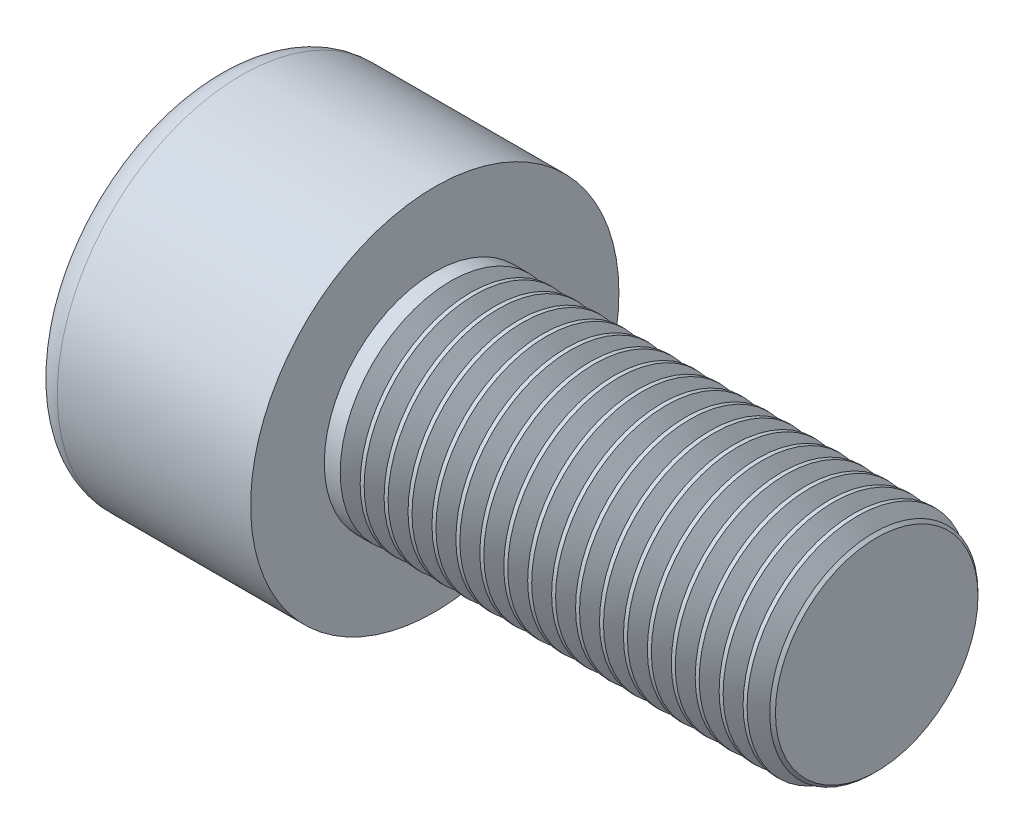
SolidWorks part; units mm, degrees
ref_plane "Front" through (0, 0, 0) normal (0, 0, 1) x (1, 0, 0)
ref_plane "Top" through (0, 0, 0) normal (0, 1, 0) x (1, 0, 0)
ref_plane "Right" through (0, 0, 0) normal (1, 0, 0) x (0, 0, -1)
sketch "Sketch1" plane through (0, 0, 0) normal (1, 0, 0) x (0, 0, -1)
  circle A0 centre (0, 0) radius 5
  dimension "dk" = 10
extrude "BaseHead" add sketch "Sketch1" along normal blind 6
sketch "Sketch2" plane through (6, 0, 0) normal (1, 0, 0) x (0, 0, -1)
  circle A0 centre (0, 0) radius 3
  dimension "d" = 6
extrude "BaseBody" add sketch "Sketch2" along normal blind 12
cosmetic thread "ThreadCosmetic1" [suppressed] parameters "b"=12, "D2"=4.917
sketch "Sketch3" plane through (0, 0, 0) normal (1, 0, 0) x (0, 0, -1)
  line L1 (2.8868, 0) -> (1.4434, 2.5)
  line L2 (1.4434, 2.5) -> (-1.4434, 2.5)
  line L3 (-1.4434, 2.5) -> (-2.8868, 0)
  line L4 (-2.8868, 0) -> (-1.4434, -2.5)
  line L5 (-1.4434, -2.5) -> (1.4434, -2.5)
  line L6 (1.4434, -2.5) -> (2.8868, 0)
  circle A0 centre (0, 0) radius 2.5 construction
  dimension "s" = 5
  dimension "e" = 5.7735
extrude "HexagonSocket" cut sketch "Sketch3" along normal blind 3
sketch "Sketch4" plane through (-4.1961, 0.75, 0) normal (0, 0, 1) x (-1, 0, 0)
  line L0 (-7.1961, 3.25) -> (-8.6395, 0.75)
  line L2 (-8.6395, 0.75) -> (-7.1961, 0.75)
  line L3 (-7.1961, 0.75) -> (-7.1961, 3.25)
  line L4 (-5.0351, 0.75) -> (0.839, 0.75) construction
  line L5 (-22.1961, 0.75) -> (-10.1961, 0.75) construction
  line L6 (-10.1961, 0.75) -> (-4.1961, 0.75) construction
  dimension "m" = 60
revolve "Cut-Revolve1" cut sketch "Sketch4" angle 360 about L4
fillet "HeadFillet" [suppressed] radius 0.25
fillet "TopFillet" radius 0.75 1 edges at (0, 0, -5)
chamfer "Chamfer1" distance 0.25 angle 45 1 edges at (18, 0, -3)
sketch "Sketch5" plane through (0, 0, 0) normal (0, 0, 1) x (1, 0, 0)
  line L0 (17.75, 2.531) -> (18.0208, 3)
  line L1 (18.0208, 3) -> (18.0208, 3.5415)
  line L2 (18.0208, 3.5415) -> (17.4793, 3.5415)
  line L3 (17.4793, 3.5415) -> (17.4793, 3)
  line L4 (17.4793, 3) -> (17.75, 2.531)
  line L5 (0, 0) -> (7.8886, 0) construction
  line L6 (17.75, -3) -> (17.75, 3) construction
  dimension "D1" = 6
  dimension "D2" = 0.5415
revolve "Cut-Revolve10" cut sketch "Sketch5" angle 360 about L5
pattern_linear "LPattern10" count 18 spacing 0.6498 along (-1, 0, 0) of "Cut-Revolve10"
equation "\"r1@TopFillet\" = \"d@Sketch2\" / 8"
equation "\"D1@Chamfer1\" = \"r@HeadFillet\""
equation "\"D1@Sketch5\" = \"d@Sketch2\""
equation "\"D2@Sketch5\" =  ( \"d@Sketch2\" - \"D2@ThreadCosmetic1\" )  / 2"
equation "\"D3@LPattern10\" = \"D2@Sketch5\" * 1.2"
equation "\"D1@LPattern10\" = \"b@ThreadCosmetic1\" / \"D3@LPattern10\""
